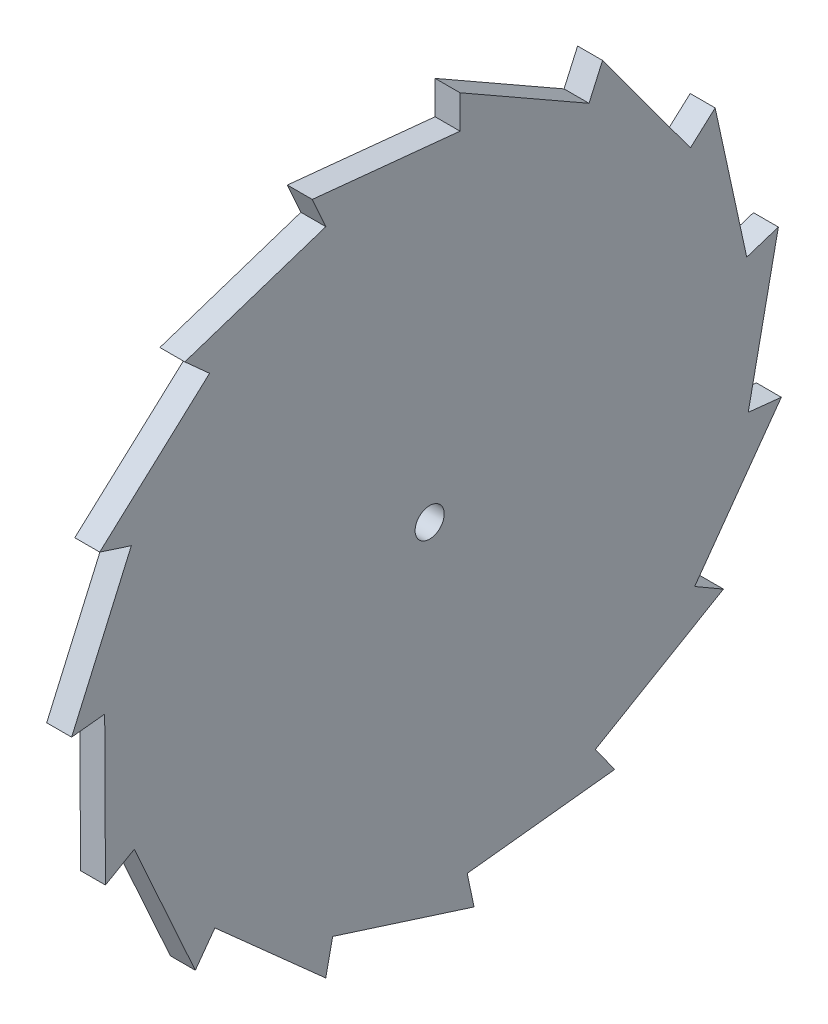
SolidWorks part; units mm, degrees
ref_plane "Front Plane" through (0, 0, 0) normal (0, 0, 1) x (1, 0, 0)
ref_plane "Top Plane" through (0, 0, 0) normal (0, 1, 0) x (1, 0, 0)
ref_plane "Right Plane" through (0, 0, 0) normal (1, 0, 0) x (0, 0, -1)
sketch "Sketch1" plane through (0, 0, 0) normal (1, 0, 0) x (0, 0, -1)
  line L0 (-28.923, 86.1596) -> (-28.923, 94.1596)
  line L1 (-28.923, 94.1596) -> (2.1046, 76.4557)
  line L2 (2.1046, 76.4557) -> (5.3585, 83.7641)
  line L3 (5.3585, 83.7641) -> (26.5028, 54.9706)
  line L4 (26.5028, 54.9706) -> (32.448, 60.3237)
  line L5 (32.448, 60.3237) -> (40.0529, 25.4194)
  line L6 (40.0529, 25.4194) -> (47.6613, 27.8916)
  line L7 (47.6613, 27.8916) -> (40.4119, -7.0882)
  line L8 (40.4119, -7.0882) -> (48.3681, -7.9245)
  line L9 (48.3681, -7.9245) -> (27.5179, -36.9315)
  line L10 (27.5179, -36.9315) -> (34.4461, -40.9315)
  line L11 (34.4461, -40.9315) -> (3.6002, -58.9502)
  line L12 (3.6002, -58.9502) -> (8.3025, -65.4224)
  line L13 (8.3025, -65.4224) -> (-27.2055, -69.3371)
  line L14 (-27.2055, -69.3371) -> (-25.5422, -77.1623)
  line L15 (-25.5422, -77.1623) -> (-59.5726, -66.2962)
  line L16 (-59.5726, -66.2962) -> (-61.2359, -74.1214)
  line L17 (-61.2359, -74.1214) -> (-87.9046, -50.3533)
  line L18 (-87.9046, -50.3533) -> (-92.6069, -56.8255)
  line L19 (-92.6069, -56.8255) -> (-107.3026, -24.2651)
  line L20 (-107.3026, -24.2651) -> (-114.2308, -28.2651)
  line L21 (-114.2308, -28.2651) -> (-114.4125, 7.4575)
  line L22 (-114.4125, 7.4575) -> (-122.3687, 6.6213)
  line L23 (-122.3687, 6.6213) -> (-108.005, 39.3295)
  line L24 (-108.005, 39.3295) -> (-115.6135, 41.8016)
  line L25 (-115.6135, 41.8016) -> (-89.188, 65.8398)
  line L26 (-89.188, 65.8398) -> (-95.1331, 71.1928)
  line L27 (-95.1331, 71.1928) -> (-61.215, 82.4046)
  line L28 (-61.215, 82.4046) -> (-64.4689, 89.7129)
  line L29 (-64.4689, 89.7129) -> (-28.923, 86.1596)
  point P0 (-36.2359, 8.321)
  point P1 (3.7316, 80.1099)
  point P5 (-36.2359, 8.321)
  point P10 (-36.2359, 8.321)
  point P64 (-36.2359, 8.321)
  dimension "D1" = 58.3983
  dimension "D3" = 8
  dimension "D4" = 25
  dimension "D2" = 15
sketch "Sketch2" plane through (0, 0, 0) normal (1, 0, 0) x (0, 0, -1)
  point P0 (-36.2359, 8.321)
extrude "Boss-Extrude1" add sketch "Sketch1" along normal blind 6 contours L0 L1 L2 L3 L4 L5 L6 L7 L8 L9 L10 L11 L12 L13 L14 L15 L16 L17 L18 L19 L20 L21 L22 L23 L24 L25 L26 L27 L28 L29
hole_wizard "Tap Drill for M8x1.0 Tap2" positions "Sketch6" profile "Sketch7" hole size "M8x1.0" standard "ANSI Metric" end condition through all
sketch "Sketch6" plane through (0, 0, 0) normal (-1, 0, 0) x (0, 0, 1)
  point P0 (36.2359, 8.321)
sketch "Sketch7" plane through (0, 8.321, 36.2359) normal (0, 1, 0) x (0, 0, 1)
  line L0 (0, 0) -> (0, 6)
  line L1 (0, 6) -> (3.5, 6)
  line L2 (3.5, 6) -> (3.5, 0)
  line L5 (3.5, 0) -> (0, 0)
  line L11 (0, -6.35) -> (0, 107.95) construction
  dimension "Thru Hole Dia." = 7
  dimension "Thru Hole Depth" = 6
